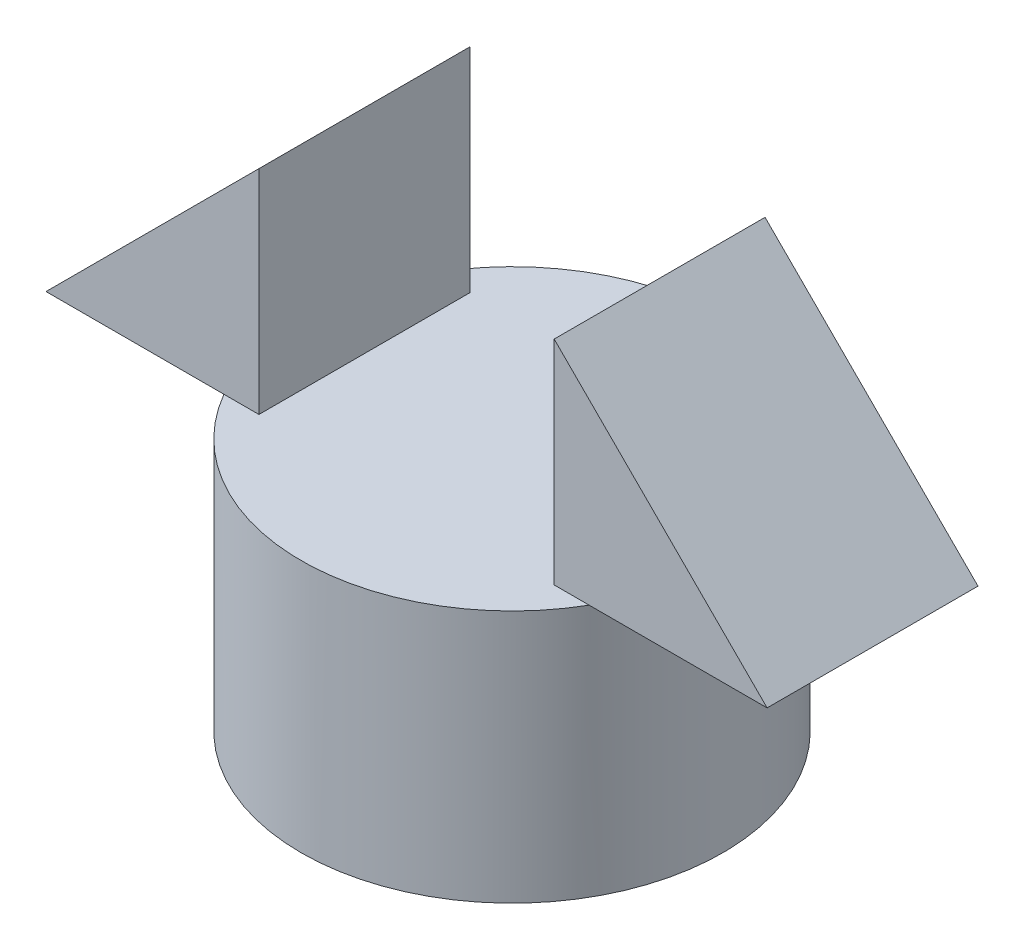
SolidWorks part; units mm, degrees
ref_plane "前视基准面" through (0, 0, 0) normal (0, 0, 1) x (1, 0, 0)
ref_plane "上视基准面" through (0, 0, 0) normal (0, 1, 0) x (1, 0, 0)
ref_plane "右视基准面" through (0, 0, 0) normal (1, 0, 0) x (0, 0, -1)
other "Configuration Table"
sketch "草图1" plane through (0, 0, 0) normal (0, 1, 0) x (1, 0, 0)
  circle A0 centre (0, 0) radius 25
  dimension "D1" = 50
extrude "凸台-拉伸1" add sketch "草图1" along normal blind 30
sketch "草图3" plane through (0, 0, 0) normal (0, 0, 1) x (1, 0, 0)
  line L0 (42.7445, 30) -> (-42.7445, 30)
  line L2 (-42.7445, 30) -> (0, 72.7445)
  line L3 (0, 72.7445) -> (42.7445, 30)
  point P3 (0, 30)
extrude "凸台-拉伸2" add sketch "草图3" along normal mid plane 25
sketch "草图4" plane through (0, 0, 0) normal (0, 0, 1) x (1, 0, 0)
  line L0 (17.5003, 30) -> (-17.5003, 30)
  line L1 (0, 72.7445) -> (17.5003, 55.2443)
  line L2 (-42.7445, 30) -> (-21.6506, 30) construction
  line L3 (-17.5003, 30) -> (-17.5003, 55.2443)
  line L4 (0, 72.7445) -> (-42.7445, 30) construction
  line L5 (-17.5003, 55.2443) -> (0, 72.7445)
  line L6 (42.7445, 30) -> (0, 72.7445) construction
  line L7 (17.5003, 55.2443) -> (17.5003, 30)
  point P3 (0, 30)
extrude "切除-拉伸1" cut sketch "草图4" against normal mid plane 38
